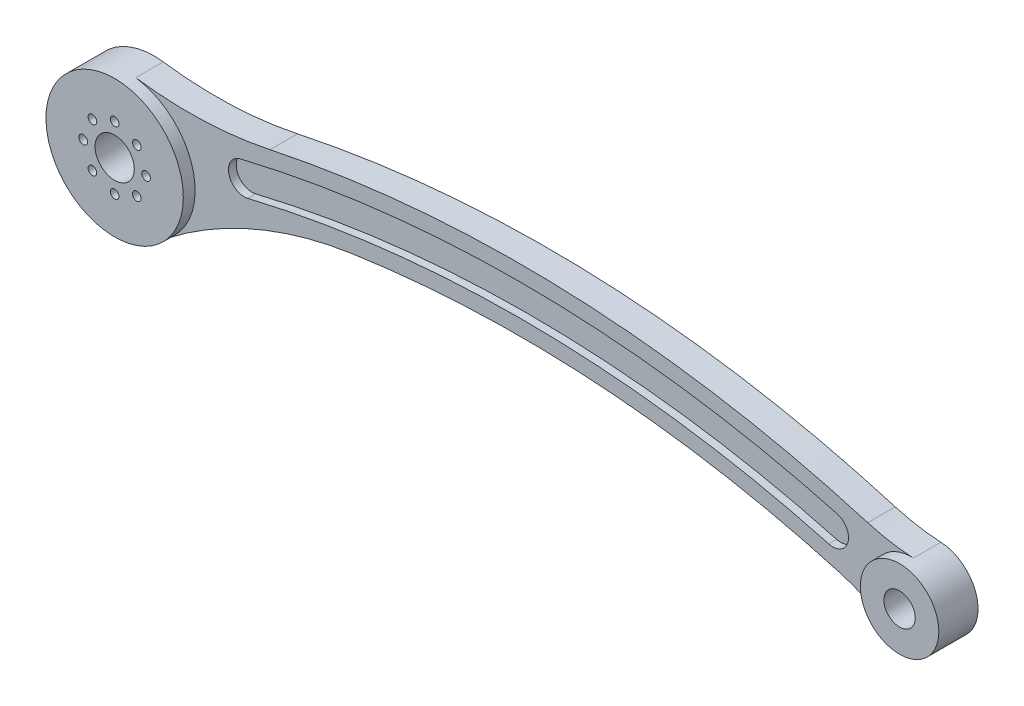
SolidWorks part; units mm, degrees
material "1060 Alloy"
ref_plane "Front Plane" through (0, 0, 0) normal (0, 0, 1) x (1, 0, 0)
ref_plane "Top Plane" through (0, 0, 0) normal (0, 1, 0) x (1, 0, 0)
ref_plane "Right Plane" through (0, 0, 0) normal (1, 0, 0) x (0, 0, -1)
sketch "Sketch1" plane through (0, 0, 0) normal (0, 0, 1) x (1, 0, 0)
  line L0 (0, 0) -> (19.0679, 6.0344) construction
  line L1 (0, 0) -> (0, 17.5) construction
  arc A0 (12.3323, 12.4163) -> (17.2734, -2.8072) centre (0, 0) ccw
  arc A2 (19.0679, 6.0344) -> (199.9996, 0.4239) centre (100.6038, -284.7506) cw construction
  arc A3 (30.9351, 4.9912) -> (178.948, 2.7667) centre (100.6038, -284.7506) cw
  arc A4 (29.0649, 12.7695) -> (181.0512, 10.4853) centre (100.6038, -284.7506) cw
  arc A5 (17.2734, -2.8072) -> (191.757, -5.2383) centre (100.6038, -284.7506) cw
  arc A6 (12.3323, 12.4163) -> (196.8729, 9.9226) centre (100.6038, -284.7506) cw
  arc A7 (-2.665, 7.5431) -> (202.6326, 7.9782) centre (100.6038, -284.7506) cw construction
  arc A8 (-1.3325, 3.7715) -> (201.3161, 4.2011) centre (100.6038, -284.7506) cw construction
  arc A9 (0, 0) -> (199.9996, 0.4239) centre (100.6038, -284.7506) cw construction
  arc A10 (1.3325, -3.7715) -> (198.6831, -3.3532) centre (100.6038, -284.7506) cw construction
  arc A11 (2.665, -7.5431) -> (197.3666, -7.1304) centre (100.6038, -284.7506) cw construction
  arc A12 (29.0649, 12.7695) -> (30.9351, 4.9912) centre (30, 8.8803) ccw
  arc A13 (178.948, 2.7667) -> (181.0512, 10.4853) centre (179.9996, 6.626) ccw
  circle A14 centre (0, 0) radius 5
  circle A15 centre (199.9996, 0.4239) radius 4
  arc A16 (191.757, -5.2383) -> (196.8729, 9.9226) centre (199.9996, 0.4239) ccw
  dimension "D1" = 35
  dimension "D2" = 20
  dimension "D4" = 4
  dimension "D6" = 306
  dimension "D7" = 8
  dimension "D9" = 310
  dimension "D11" = 30
  dimension "D12" = 20
  dimension "D14" = 8
  dimension "D15" = 10
  dimension "D3" = 200
  dimension "D10" = 72.439
  dimension "D13" = 20
  dimension "D5" = 4
  dimension "D8" = 8
extrude "Boss-Extrude1" add sketch "Sketch1" along normal blind 10
fillet "Fillet1" radius 100 2 edges at (12.3323, 12.4163, 5) (17.2734, -2.8072, 5)
fillet "Fillet3" radius 50 2 edges at (191.757, -5.2383, 5) (196.8729, 9.9226, 5)
sketch "Sketch2" plane through (0, 0, 0) normal (0, 0, -1) x (-1, 0, 0)
  arc A0 (-30.9351, 4.9912) -> (-29.0649, 12.7695) centre (-30, 8.8803) ccw construction
  arc A1 (-29.0649, 12.7695) -> (-181.0512, 10.4853) centre (-100.6038, -284.7506) ccw construction
  arc A2 (-30.9351, 4.9912) -> (-178.948, 2.7667) centre (-100.6038, -284.7506) ccw construction
  arc A3 (-181.0512, 10.4853) -> (-178.948, 2.7667) centre (-179.9996, 6.626) ccw construction
  arc A4 (-30.9351, 4.9912) -> (-29.0649, 12.7695) centre (-30, 8.8803) ccw
  arc A5 (-29.0649, 12.7695) -> (-181.0512, 10.4853) centre (-100.6038, -284.7506) ccw
  arc A6 (-30.9351, 4.9912) -> (-178.948, 2.7667) centre (-100.6038, -284.7506) ccw
  arc A7 (-181.0512, 10.4853) -> (-178.948, 2.7667) centre (-179.9996, 6.626) ccw
extrude "Boss-Extrude2" add sketch "Sketch2" against normal blind 5
sketch "Sketch3" plane through (0, 0, 10) normal (0, 0, 1) x (1, 0, 0)
  arc A0 (10.7199, -13.8324) -> (2.3745, 17.3382) centre (0, 0) ccw
  arc A1 (200.5207, 10.4103) -> (194.6242, -8.0085) centre (199.9996, 0.4239) ccw
  arc A8 (194.6242, -8.0085) -> (200.5207, 10.4103) centre (199.9996, 0.4239) ccw
  arc A9 (188.887, 12.4128) -> (200.5207, 10.4103) centre (203.1262, 60.3424) ccw
  arc A10 (188.887, 12.4128) -> (36.5918, 18.5685) centre (100.6038, -284.7506) ccw
  arc A11 (2.3745, 17.3382) -> (36.5918, 18.5685) centre (15.9428, 116.4134) ccw
  arc A12 (2.3745, 17.3382) -> (10.7199, -13.8324) centre (0, 0) ccw
  arc A13 (57.22, 6.0309) -> (10.7199, -13.8324) centre (71.9764, -92.8744) ccw
  arc A14 (181.5067, -2.1011) -> (57.22, 6.0309) centre (100.6038, -284.7506) ccw
  arc A15 (194.6242, -8.0085) -> (181.5067, -2.1011) centre (167.7477, -50.1707) ccw
  arc A17 (188.887, 12.4128) -> (200.5207, 10.4103) centre (203.1262, 60.3424) ccw
  arc A18 (188.887, 12.4128) -> (36.5918, 18.5685) centre (100.6038, -284.7506) ccw
  arc A19 (2.3745, 17.3382) -> (36.5918, 18.5685) centre (15.9428, 116.4134) ccw
  arc A21 (57.22, 6.0309) -> (10.7199, -13.8324) centre (71.9764, -92.8744) ccw
  arc A22 (181.5067, -2.1011) -> (57.22, 6.0309) centre (100.6038, -284.7506) ccw
  arc A23 (194.6242, -8.0085) -> (181.5067, -2.1011) centre (167.7477, -50.1707) ccw
  dimension "D1" = 0
extrude "Cut-Extrude1" cut sketch "Sketch3" against normal blind 3
hole_wizard "M2 Clearance Hole2" positions "Sketch6" profile "Sketch7" hole size "M2" standard "ANSI Metric" end condition up to next
sketch "Sketch6" plane through (0, 0, 10) normal (0, 0, 1) x (1, 0, 0)
  point P0 (0, 8)
  point P9 (5.6569, 5.6569)
  point P10 (8, 0)
  point P11 (5.6569, -5.6569)
  point P12 (0, -8)
  point P13 (-5.6569, -5.6569)
  point P14 (-8, 0)
  point P15 (-5.6569, 5.6569)
  dimension "D1" = 8
  dimension "D3" = 8
  dimension "D4" = 45
  dimension "D2" = 8
sketch "Sketch7" plane through (0, 8, 10) normal (1, 0, 0) x (0, -1, 0)
  line L0 (0, 0) -> (0, 10)
  line L1 (0, 10) -> (1.1, 10)
  line L2 (1.1, 10) -> (1.1, 0)
  line L5 (1.1, 0) -> (0, 0)
  line L11 (0, -6.35) -> (0, 107.95) construction
  dimension "Thru Hole Dia." = 2.2
  dimension "Thru Hole Depth" = 10
